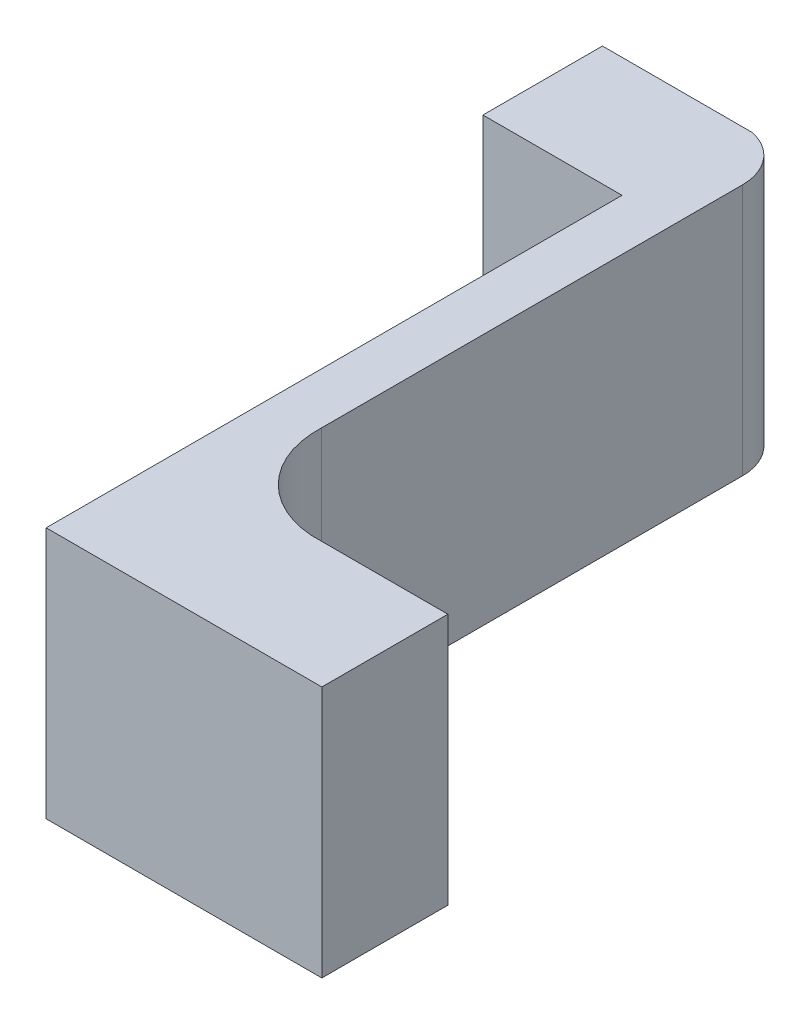
SolidWorks part; units mm, degrees
ref_plane "Front" through (0, 0, 0) normal (0, 0, 1) x (1, 0, 0)
ref_plane "Top" through (0, 0, 0) normal (0, 1, 0) x (1, 0, 0)
ref_plane "Right" through (0, 0, 0) normal (1, 0, 0) x (0, 0, -1)
sketch "Sketch1" plane through (0, 0, 0) normal (0, 1, 0) x (1, 0, 0)
  line L0 (0.1629, -1.0402) -> (0.379, -1.0402)
  line L6 (-0.0585, -1.2402) -> (0.2029, -1.2402)
  line L11 (-0.0585, -0.3263) -> (-0.2793, -0.3263)
  line L17 (0.0227, -0.8976) -> (0.0227, -0.2159)
  line L23 (-0.0585, -1.2402) -> (0.2029, -1.2402)
  line L29 (-0.0585, -0.3263) -> (-0.0585, -1.2402)
  line L30 (0.2029, -1.2402) -> (0.379, -1.2402)
  line L36 (0.379, -1.2402) -> (0.379, -1.0402)
  line L38 (-0.2793, -0.3263) -> (-0.2793, -0.1366)
  line L39 (-0.2793, -0.1366) -> (-0.0412, -0.1366)
  arc A1 (0.0227, -0.8844) -> (0.1629, -1.0402) centre (0.172, -0.891) ccw
  arc A2 (0.0227, -0.2159) -> (-0.0412, -0.1366) centre (-0.0585, -0.2159) ccw
  point P9 (0.0438, -0.5402)
  point P12 (0.2029, -0.2256)
extrude "Boss-Extrude2" add sketch "Sketch1" along normal blind 0.4
